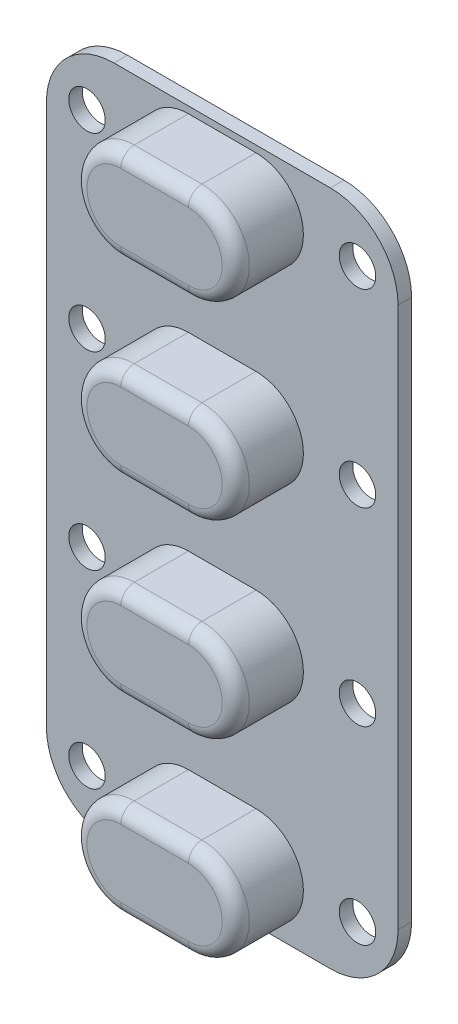
SolidWorks part; units mm, degrees
ref_plane "Front Plane" through (0, 0, 0) normal (0, 0, 1) x (1, 0, 0)
ref_plane "Top Plane" through (0, 0, 0) normal (0, 1, 0) x (1, 0, 0)
ref_plane "Right Plane" through (0, 0, 0) normal (1, 0, 0) x (0, 0, -1)
sketch "Sketch1" plane through (0, 0, 0) normal (0, 0, 1) x (1, 0, 0)
  line L1 (13, 25) -> (-13, 25)
  line L2 (13, 25) -> (13, -25)
  line L3 (13, -25) -> (-13, -25)
  line L4 (-13, 25) -> (-13, -25)
  line L5 (13, 25) -> (-13, -25) construction
  line L6 (13, -25) -> (-13, 25) construction
  circle A1 centre (10, -21) radius 1.35
  circle A9 centre (10, -7) radius 1.35
  circle A10 centre (10, 7) radius 1.35
  circle A11 centre (10, 21) radius 1.35
  circle A12 centre (-10, -7) radius 1.35
  circle A13 centre (-10, 7) radius 1.35
  circle A14 centre (-10, 21) radius 1.35
  circle A15 centre (-10, -21) radius 1.35
  point P0 (0, 0)
  dimension "D5" = 2.7
  dimension "D1" = 26
  dimension "D2" = 50
  dimension "D3" = 10
  dimension "D4" = 21
  dimension "D8" = 14
  dimension "D9" = 20
  dimension "D6" = 4
  dimension "D7" = 2
extrude "Boss-Extrude1" add sketch "Sketch1" along normal blind 1
sketch "Sketch2" plane through (0, 0, 1) normal (0, 0, 1) x (1, 0, 0)
  line L0 (-2.5, 21) -> (2.5, 21) construction
  line L1 (-2.5, 24.5) -> (2.5, 24.5)
  line L2 (-2.5, 17.5) -> (2.5, 17.5)
  line L3 (-2.5, 3.5) -> (2.5, 3.5)
  line L4 (-2.5, 10.5) -> (2.5, 10.5)
  line L5 (-2.5, 7) -> (2.5, 7) construction
  line L6 (-2.5, -10.5) -> (2.5, -10.5)
  line L7 (-2.5, -3.5) -> (2.5, -3.5)
  line L8 (-2.5, -7) -> (2.5, -7) construction
  line L9 (-2.5, -24.5) -> (2.5, -24.5)
  line L10 (-2.5, -17.5) -> (2.5, -17.5)
  line L11 (-2.5, -21) -> (2.5, -21) construction
  arc A0 (-2.5, 24.5) -> (-2.5, 17.5) centre (-2.5, 21) ccw
  arc A1 (2.5, 17.5) -> (2.5, 24.5) centre (2.5, 21) ccw
  arc A2 (-2.5, 10.5) -> (-2.5, 3.5) centre (-2.5, 7) ccw
  arc A3 (2.5, 3.5) -> (2.5, 10.5) centre (2.5, 7) ccw
  arc A4 (-2.5, -3.5) -> (-2.5, -10.5) centre (-2.5, -7) ccw
  arc A5 (2.5, -10.5) -> (2.5, -3.5) centre (2.5, -7) ccw
  arc A6 (-2.5, -17.5) -> (-2.5, -24.5) centre (-2.5, -21) ccw
  arc A7 (2.5, -24.5) -> (2.5, -17.5) centre (2.5, -21) ccw
  point P2 (0, 21)
  point P10 (0, 7)
  point P18 (0, -7)
  point P25 (0, -21)
  dimension "D2" = 3.5
  dimension "D1" = 5
  dimension "D3" = 21
  dimension "D5" = 14
  dimension "D4" = 4
extrude "Boss-Extrude2" add sketch "Sketch2" along normal blind 5
fillet "Fillet1" radius 1 16 edges at (0, -17.5, 6) (6, -21, 6) (0, -24.5, 6) (-6, -21, 6) (0, -3.5, 6) (6, -7, 6) (0, -10.5, 6) (-6, -7, 6) (0, 10.5, 6) (6, 7, 6) (0, 3.5, 6) (-6, 7, 6) (0, 24.5, 6) (6, 21, 6) (0, 17.5, 6) (-6, 21, 6)
fillet "Fillet2" radius 5 4 edges at (13, 25, 0.5) (-13, 25, 0.5) (13, -25, 0.5) (-13, -25, 0.5)
sketch "Sketch3" plane through (0, 0, 0) normal (0, 0, -1) x (-1, 0, 0)
  line L0 (10, 21) -> (-10, 21) construction
  line L1 (-10, 7) -> (10, 7) construction
  line L2 (10, -7) -> (-10, -7) construction
  line L3 (-10, -21) -> (10, -21) construction
  circle A0 centre (0, 21) radius 2.625
  circle A1 centre (0, 7) radius 2.625
  circle A2 centre (0, -7) radius 2.625
  circle A3 centre (0, -21) radius 2.625
  dimension "D1" = 5.25
extrude "Cut-Extrude1" cut sketch "Sketch3" against normal blind 3 contours A0 | A1 | A2 | A3
